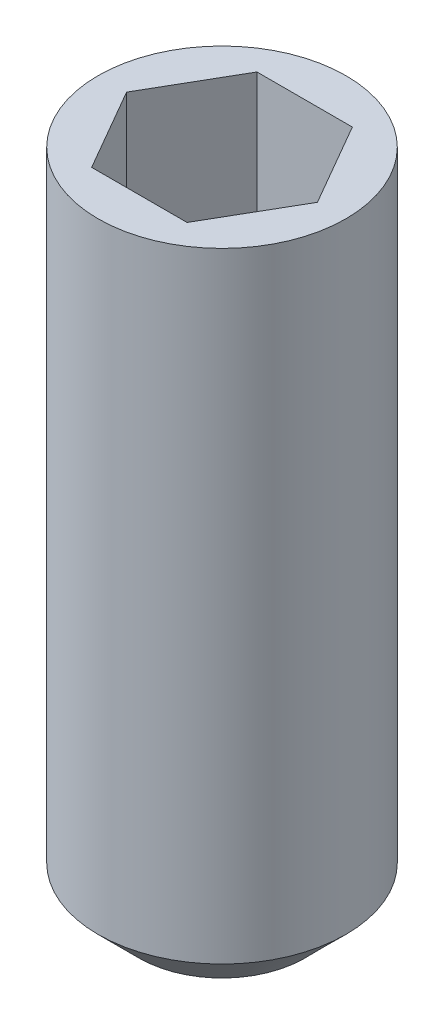
SolidWorks part; units mm, degrees
ref_plane "Front Plane" through (0, 0, 0) normal (0, 0, 1) x (1, 0, 0)
ref_plane "Top Plane" through (0, 0, 0) normal (0, 1, 0) x (1, 0, 0)
ref_plane "Right Plane" through (0, 0, 0) normal (1, 0, 0) x (0, 0, -1)
sketch "Sketch1" plane through (0, 0, 0) normal (0, 1, 0) x (1, 0, 0)
  circle A0 centre (0, 0) radius 1.5
  dimension "D1" = 3
extrude "Boss-Extrude1" add sketch "Sketch1" along normal blind 8
chamfer "Chamfer1" distance 0.5 angle 45 1 edges at (0, 0, 1.5)
sketch "Sketch2" plane through (0, 8, 0) normal (0, 1, 0) x (1, 0, 0)
  line L1 (0.5774, -1) -> (1.1547, 0)
  line L2 (1.1547, 0) -> (0.5774, 1)
  line L3 (0.5774, 1) -> (-0.5774, 1)
  line L4 (-0.5774, 1) -> (-1.1547, 0)
  line L5 (-1.1547, 0) -> (-0.5774, -1)
  line L6 (-0.5774, -1) -> (0.5774, -1)
  circle A0 centre (0, 0) radius 1 construction
  dimension "D1" = 2
extrude "Cut-Extrude1" cut sketch "Sketch2" against normal blind 1.5
